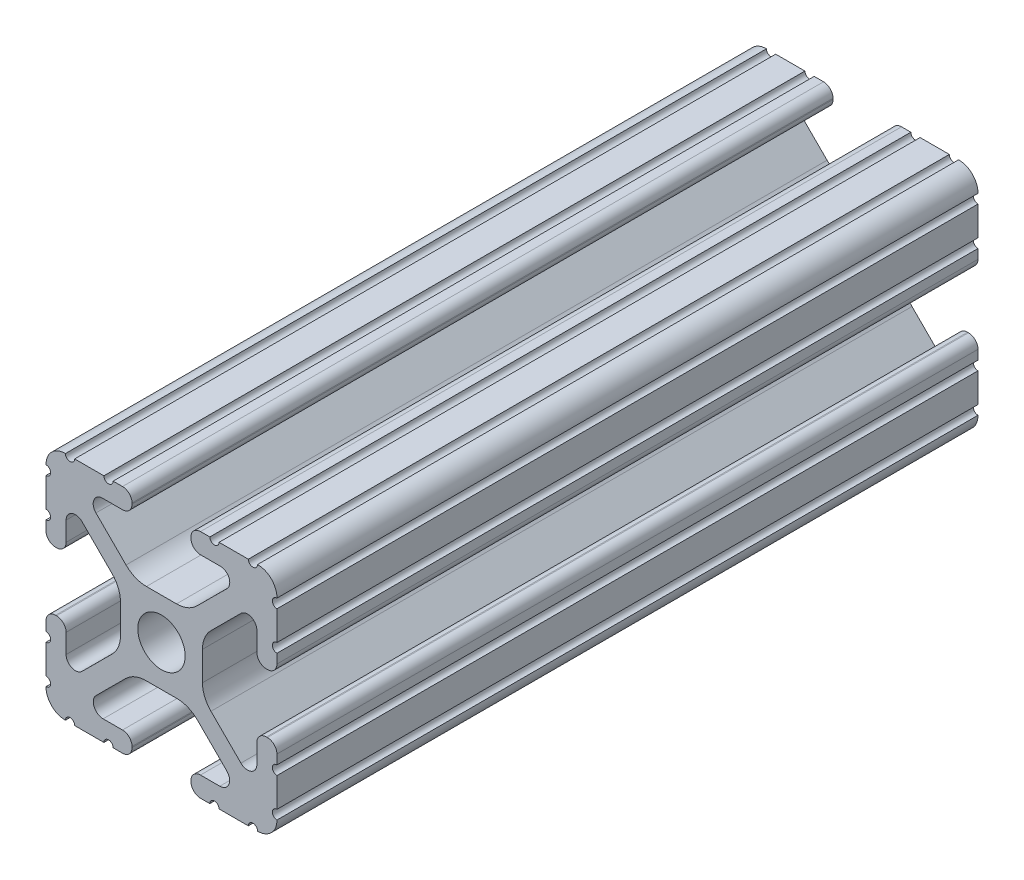
SolidWorks part; units mm, degrees
ref_plane "Front Plane" through (0, 0, 0) normal (0, 0, 1) x (1, 0, 0)
ref_plane "Top Plane" through (0, 0, 0) normal (0, 1, 0) x (1, 0, 0)
ref_plane "Right Plane" through (0, 0, 0) normal (1, 0, 0) x (0, 0, -1)
sketch "Sketch1" plane through (0, 0, 0) normal (0, 0, 1) x (1, 0, 0)
  line L0 (-7.207, 8.7244) -> (-3.8983, 5.4232)
  line L1 (-4.2875, 10.4902) -> (-6.4768, 10.4902)
  line L2 (-3.2385, 11.651) -> (-3.2385, 11.5392)
  line L3 (-5.3171, 12.7) -> (-4.2875, 12.7)
  line L4 (0, 13.4005) -> (0, -14.8534) construction
  line L5 (12.7, 0) -> (-13.9989, 0) construction
  line L6 (-9.5504, 12.7) -> (-6.3331, 12.7)
  line L7 (-12.7, 6.3331) -> (-12.7, 9.5504)
  line L8 (-12.7, 4.2875) -> (-12.7, 5.3171)
  line L9 (-11.5392, 3.2385) -> (-11.651, 3.2385)
  line L10 (-10.4902, 6.4021) -> (-10.4902, 4.2875)
  line L11 (-5.441, 3.8408) -> (-8.7371, 7.1294)
  line L12 (-4.5085, -1.5932) -> (-4.5085, 1.5932)
  line L13 (-1.7093, -4.4958) -> (1.7093, -4.4958)
  line L14 (3.9523, -5.4237) -> (7.1797, -8.6452)
  line L15 (6.4164, -10.4902) -> (4.2875, -10.4902)
  line L16 (3.2385, -11.5392) -> (3.2385, -11.651)
  line L17 (4.2875, -12.7) -> (5.3171, -12.7)
  line L18 (6.3331, -12.7) -> (9.5504, -12.7)
  line L19 (12.7, -9.5504) -> (12.7, -6.3331)
  line L20 (12.7, -5.3171) -> (12.7, -4.2875)
  line L21 (11.651, -3.2385) -> (11.5392, -3.2385)
  line L22 (10.4902, -4.2875) -> (10.4902, -6.4021)
  line L23 (8.7371, -7.1294) -> (5.441, -3.8408)
  line L24 (4.5085, -1.5932) -> (4.5085, 1.5932)
  line L25 (5.441, 3.8408) -> (8.7371, 7.1294)
  line L26 (10.4902, 6.4021) -> (10.4902, 4.2875)
  line L27 (11.5392, 3.2385) -> (11.651, 3.2385)
  line L28 (12.7, 4.2875) -> (12.7, 5.3171)
  line L29 (12.7, 6.3331) -> (12.7, 9.5504)
  line L30 (9.5504, 12.7) -> (6.3331, 12.7)
  line L31 (5.3171, 12.7) -> (4.2875, 12.7)
  line L32 (3.2385, 11.651) -> (3.2385, 11.5392)
  line L33 (4.2875, 10.4902) -> (6.4768, 10.4902)
  line L34 (7.207, 8.7244) -> (3.8983, 5.4232)
  line L35 (1.6558, 4.4958) -> (-1.6558, 4.4958)
  line L36 (-8.7371, -7.1294) -> (-5.441, -3.8408)
  line L37 (-10.4902, -4.2875) -> (-10.4902, -6.4021)
  line L38 (-11.651, -3.2385) -> (-11.5392, -3.2385)
  line L39 (-12.7, -5.3171) -> (-12.7, -4.2875)
  line L40 (-12.7, -9.5504) -> (-12.7, -6.3331)
  line L41 (-6.3331, -12.7) -> (-9.5504, -12.7)
  line L42 (-4.2875, -12.7) -> (-5.3171, -12.7)
  line L43 (-3.2385, -11.5392) -> (-3.2385, -11.651)
  line L44 (-6.4164, -10.4902) -> (-4.2875, -10.4902)
  line L45 (-3.9523, -5.4237) -> (-7.1797, -8.6452)
  arc A0 (-7.207, 8.7244) -> (-6.4768, 10.4902) centre (-6.4768, 9.4563) cw
  arc A1 (-3.2385, 11.5392) -> (-4.2875, 10.4902) centre (-4.2875, 11.5392) cw
  arc A2 (-4.2875, 12.7) -> (-3.2385, 11.651) centre (-4.2875, 11.651) cw
  arc A3 (-5.3171, 12.7) -> (-6.3331, 12.7) centre (-5.8251, 12.7) cw
  arc A4 (-9.5504, 12.7) -> (-10.5664, 12.6998) centre (-10.0584, 12.7) cw
  arc A5 (-12.6998, 10.5664) -> (-10.5664, 12.6998) centre (-10.5918, 10.5918) cw
  arc A6 (-12.6998, 10.5664) -> (-12.7, 9.5504) centre (-12.7, 10.0584) cw
  arc A7 (-12.7, 6.3331) -> (-12.7, 5.3171) centre (-12.7, 5.8251) cw
  arc A8 (-11.651, 3.2385) -> (-12.7, 4.2875) centre (-11.651, 4.2875) cw
  arc A9 (-10.4902, 4.2875) -> (-11.5392, 3.2385) centre (-11.5392, 4.2875) cw
  circle A10 centre (0, 0) radius 2.6035
  arc A11 (-10.4902, 6.4021) -> (-8.7371, 7.1294) centre (-9.4628, 6.4021) cw
  arc A12 (-5.441, 3.8408) -> (-4.5085, 1.5932) centre (-7.6835, 1.5932) cw
  arc A13 (-4.5085, -1.5932) -> (-5.441, -3.8408) centre (-7.6835, -1.5932) cw
  arc A14 (-8.7371, -7.1294) -> (-10.4902, -6.4021) centre (-9.4628, -6.4021) cw
  arc A15 (-1.7093, -4.4958) -> (-3.9523, -5.4237) centre (-1.7093, -7.6708) ccw
  arc A16 (3.9523, -5.4237) -> (1.7093, -4.4958) centre (1.7093, -7.6708) ccw
  arc A17 (6.4164, -10.4902) -> (7.1797, -8.6452) centre (6.4164, -9.4098) ccw
  arc A18 (4.2875, -10.4902) -> (3.2385, -11.5392) centre (4.2875, -11.5392) ccw
  arc A19 (3.2385, -11.651) -> (4.2875, -12.7) centre (4.2875, -11.651) ccw
  arc A20 (6.3331, -12.7) -> (5.3171, -12.7) centre (5.8251, -12.7) ccw
  arc A21 (10.5664, -12.6998) -> (9.5504, -12.7) centre (10.0584, -12.7) ccw
  arc A22 (10.5664, -12.6998) -> (12.6998, -10.5664) centre (10.5918, -10.5918) ccw
  arc A23 (12.7, -9.5504) -> (12.6998, -10.5664) centre (12.7, -10.0584) ccw
  arc A24 (12.7, -5.3171) -> (12.7, -6.3331) centre (12.7, -5.8251) ccw
  arc A25 (12.7, -4.2875) -> (11.651, -3.2385) centre (11.651, -4.2875) ccw
  arc A26 (11.5392, -3.2385) -> (10.4902, -4.2875) centre (11.5392, -4.2875) ccw
  arc A27 (8.7371, -7.1294) -> (10.4902, -6.4021) centre (9.4628, -6.4021) ccw
  arc A28 (4.5085, -1.5932) -> (5.441, -3.8408) centre (7.6835, -1.5932) ccw
  arc A29 (5.441, 3.8408) -> (4.5085, 1.5932) centre (7.6835, 1.5932) ccw
  arc A30 (10.4902, 6.4021) -> (8.7371, 7.1294) centre (9.4628, 6.4021) ccw
  arc A31 (10.4902, 4.2875) -> (11.5392, 3.2385) centre (11.5392, 4.2875) ccw
  arc A32 (11.651, 3.2385) -> (12.7, 4.2875) centre (11.651, 4.2875) ccw
  arc A33 (12.7, 6.3331) -> (12.7, 5.3171) centre (12.7, 5.8251) ccw
  arc A34 (12.6998, 10.5664) -> (12.7, 9.5504) centre (12.7, 10.0584) ccw
  arc A35 (12.6998, 10.5664) -> (10.5664, 12.6998) centre (10.5918, 10.5918) ccw
  arc A36 (9.5504, 12.7) -> (10.5664, 12.6998) centre (10.0584, 12.7) ccw
  arc A37 (5.3171, 12.7) -> (6.3331, 12.7) centre (5.8251, 12.7) ccw
  arc A38 (4.2875, 12.7) -> (3.2385, 11.651) centre (4.2875, 11.651) ccw
  arc A39 (3.2385, 11.5392) -> (4.2875, 10.4902) centre (4.2875, 11.5392) ccw
  arc A40 (7.207, 8.7244) -> (6.4768, 10.4902) centre (6.4768, 9.4563) ccw
  arc A41 (1.6558, 4.4958) -> (3.8983, 5.4232) centre (1.6558, 7.6708) ccw
  arc A42 (-1.6558, 4.4958) -> (-3.8983, 5.4232) centre (-1.6558, 7.6708) cw
  arc A43 (-11.5392, -3.2385) -> (-10.4902, -4.2875) centre (-11.5392, -4.2875) cw
  arc A44 (-12.7, -4.2875) -> (-11.651, -3.2385) centre (-11.651, -4.2875) cw
  arc A45 (-12.7, -5.3171) -> (-12.7, -6.3331) centre (-12.7, -5.8251) cw
  arc A46 (-12.7, -9.5504) -> (-12.6998, -10.5664) centre (-12.7, -10.0584) cw
  arc A47 (-10.5664, -12.6998) -> (-12.6998, -10.5664) centre (-10.5918, -10.5918) cw
  arc A48 (-10.5664, -12.6998) -> (-9.5504, -12.7) centre (-10.0584, -12.7) cw
  arc A49 (-6.3331, -12.7) -> (-5.3171, -12.7) centre (-5.8251, -12.7) cw
  arc A50 (-3.2385, -11.651) -> (-4.2875, -12.7) centre (-4.2875, -11.651) cw
  arc A51 (-4.2875, -10.4902) -> (-3.2385, -11.5392) centre (-4.2875, -11.5392) cw
  arc A52 (-6.4164, -10.4902) -> (-7.1797, -8.6452) centre (-6.4164, -9.4098) cw
  dimension "D1" = 5.207
  dimension "D9" = 14.859
  dimension "D2" = 25.4
  dimension "D3" = 12.7
  dimension "D4" = 6.477
  dimension "D5" = 8.2042
  dimension "D6" = 9.017
  dimension "D8" = 2.2098
  dimension "D10" = 2.2098
extrude "Extrude1" add sketch "Sketch1" against normal blind 77.1
